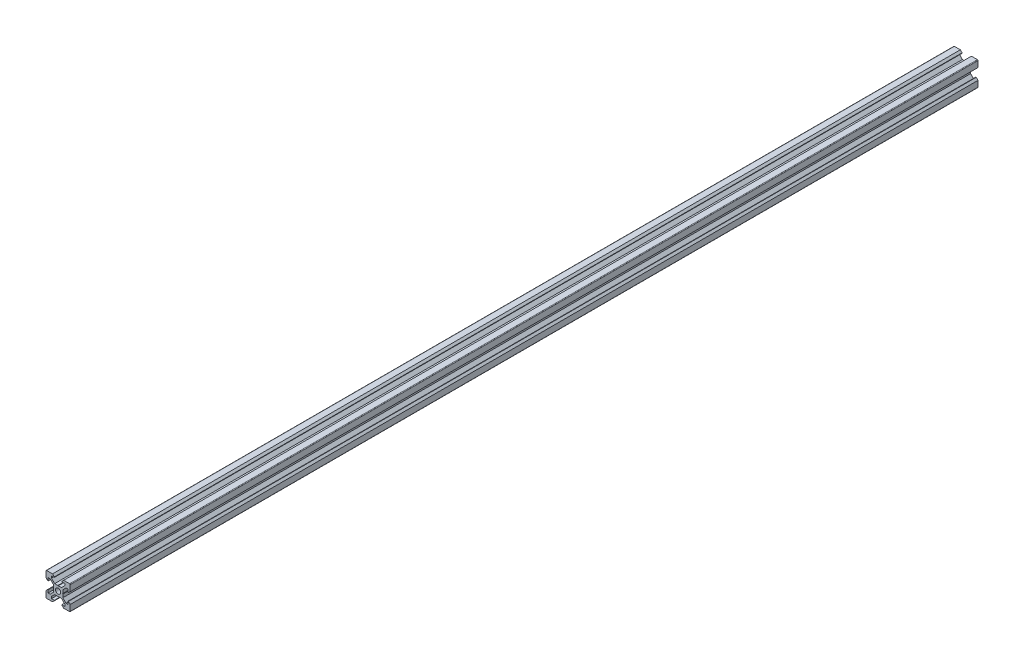
SolidWorks part; units mm, degrees
material "6061-T6 (SS)"
ref_plane "Front Plane" through (0, 0, 0) normal (0, 0, 1) x (1, 0, 0)
ref_plane "Top Plane" through (0, 0, 0) normal (0, 1, 0) x (1, 0, 0)
ref_plane "Right Plane" through (0, 0, 0) normal (1, 0, 0) x (0, 0, -1)
sketch "Sketch1" plane through (0, 0, 0) normal (0, 0, 1) x (1, 0, 0)
  line L1 (9.5, -10) -> (-9.5, -10)
  line L2 (10, -9.5) -> (10, 9.5)
  line L3 (9.5, 10) -> (-9.5, 10)
  line L4 (-10, -9.5) -> (-10, 9.5)
  line L5 (10, -10) -> (-10, 10) construction
  line L6 (10, 10) -> (-10, -10) construction
  circle A0 centre (0, 0) radius 2.1
  arc A1 (-9.5, 10) -> (-10, 9.5) centre (-9.5, 9.5) ccw
  arc A2 (10, 9.5) -> (9.5, 10) centre (9.5, 9.5) ccw
  arc A3 (9.5, -10) -> (10, -9.5) centre (9.5, -9.5) ccw
  arc A4 (-9.5, -10) -> (-10, -9.5) centre (-9.5, -9.5) cw
  point P0 (0, 0)
  line B0 (0, 0) -> (0, 10) construction
  line B1 (0, 3.69) -> (-0.21, 3.9)
  line B2 (-0.21, 3.9) -> (-2.8393, 3.9)
  line B3 (-2.8393, 3.9) -> (-5.5, 6.5607)
  line B4 (-5.5, 6.5607) -> (-5.5, 8.2)
  line B5 (-5.5, 8.2) -> (-3.125, 8.2)
  line B6 (-3.125, 8.2) -> (-3.125, 8.545)
  line B7 (-3.125, 8.545) -> (-4.58, 10)
  line B8 (-4.58, 10) -> (4.58, 10)
  line B9 (0, 0) -> (-5.9132, 5.9132) construction
  line B10 (3.125, 8.545) -> (4.58, 10)
  line B11 (3.125, 8.2) -> (3.125, 8.545)
  line B12 (5.5, 8.2) -> (3.125, 8.2)
  line B13 (5.5, 6.5607) -> (5.5, 8.2)
  line B14 (2.8393, 3.9) -> (5.5, 6.5607)
  line B15 (0.21, 3.9) -> (2.8393, 3.9)
  line B16 (0, 3.69) -> (0.21, 3.9)
  line B17 (0, 0) -> (-10, 0) construction
  line B18 (-3.69, 0) -> (-3.9, -0.21)
  line B19 (-3.9, -0.21) -> (-3.9, -2.8393)
  line B20 (-3.9, -2.8393) -> (-6.5607, -5.5)
  line B21 (-6.5607, -5.5) -> (-8.2, -5.5)
  line B22 (-8.2, -5.5) -> (-8.2, -3.125)
  line B23 (-8.2, -3.125) -> (-8.545, -3.125)
  line B24 (-8.545, -3.125) -> (-10, -4.58)
  line B25 (-10, -4.58) -> (-10, 4.58)
  line B26 (0, 0) -> (-5.9132, -5.9132) construction
  line B27 (-8.545, 3.125) -> (-10, 4.58)
  line B28 (-8.2, 3.125) -> (-8.545, 3.125)
  line B29 (-8.2, 5.5) -> (-8.2, 3.125)
  line B30 (-6.5607, 5.5) -> (-8.2, 5.5)
  line B31 (-3.9, 2.8393) -> (-6.5607, 5.5)
  line B32 (-3.9, 0.21) -> (-3.9, 2.8393)
  line B33 (-3.69, 0) -> (-3.9, 0.21)
  line B34 (0, 0) -> (0, -10) construction
  line B35 (0, -3.69) -> (0.21, -3.9)
  line B36 (0.21, -3.9) -> (2.8393, -3.9)
  line B37 (2.8393, -3.9) -> (5.5, -6.5607)
  line B38 (5.5, -6.5607) -> (5.5, -8.2)
  line B39 (5.5, -8.2) -> (3.125, -8.2)
  line B40 (3.125, -8.2) -> (3.125, -8.545)
  line B41 (3.125, -8.545) -> (4.58, -10)
  line B42 (4.58, -10) -> (-4.58, -10)
  line B43 (0, 0) -> (5.9132, -5.9132) construction
  line B44 (-3.125, -8.545) -> (-4.58, -10)
  line B45 (-3.125, -8.2) -> (-3.125, -8.545)
  line B46 (-5.5, -8.2) -> (-3.125, -8.2)
  line B47 (-5.5, -6.5607) -> (-5.5, -8.2)
  line B48 (-2.8393, -3.9) -> (-5.5, -6.5607)
  line B49 (-0.21, -3.9) -> (-2.8393, -3.9)
  line B50 (0, -3.69) -> (-0.21, -3.9)
  line B51 (0, 0) -> (10, 0) construction
  line B52 (3.69, 0) -> (3.9, 0.21)
  line B53 (3.9, 0.21) -> (3.9, 2.8393)
  line B54 (3.9, 2.8393) -> (6.5607, 5.5)
  line B55 (6.5607, 5.5) -> (8.2, 5.5)
  line B56 (8.2, 5.5) -> (8.2, 3.125)
  line B57 (8.2, 3.125) -> (8.545, 3.125)
  line B58 (8.545, 3.125) -> (10, 4.58)
  line B59 (10, 4.58) -> (10, -4.58)
  line B60 (0, 0) -> (5.9132, 5.9132) construction
  line B61 (8.545, -3.125) -> (10, -4.58)
  line B62 (8.2, -3.125) -> (8.545, -3.125)
  line B63 (8.2, -5.5) -> (8.2, -3.125)
  line B64 (6.5607, -5.5) -> (8.2, -5.5)
  line B65 (3.9, -2.8393) -> (6.5607, -5.5)
  line B66 (3.9, -0.21) -> (3.9, -2.8393)
  line B67 (3.69, 0) -> (3.9, -0.21)
  dimension "D1" = 4.2
  dimension "D3" = 0.5
  dimension "D2" = 20
sketch_block_instance "V Slot 1-4"
sketch_block "V Slot 1" parameters "D1"=10, "D2"=11, "D3"=4.3, "D4"=1.8, "D5"=0.21, "D6"=45, "D7"=9.16, "D8"=1.5, "D9"=6.25
sketch_block_instance "V Slot 1-5"
sketch_block_instance "V Slot 1-6"
sketch_block_instance "V Slot 1-7"
extrude "Boss-Extrude1" add sketch "Sketch1" along normal blind 750 contours B67 B52 B53 B54 B55 B56 B57 B58 L2 A2 L3 B10 B11 B12 B13 B14 B15 B16 B1 B2 B3 B4 B5 B6 B7 A1 L4 B27 B28 B29 B30 B31 B32 B33 B18 B19 B20 B21 B22 B23 B24 A4 L1 B44 B45 B46 B47 B48 B49
ref_plane "Plane1" through (0, 0, 0) normal (-1, 0, 0) x (0, 0, 1)
ref_plane "Plane2" through (0, 0, 0) normal (0, -1, 0) x (-1, 0, 0)
